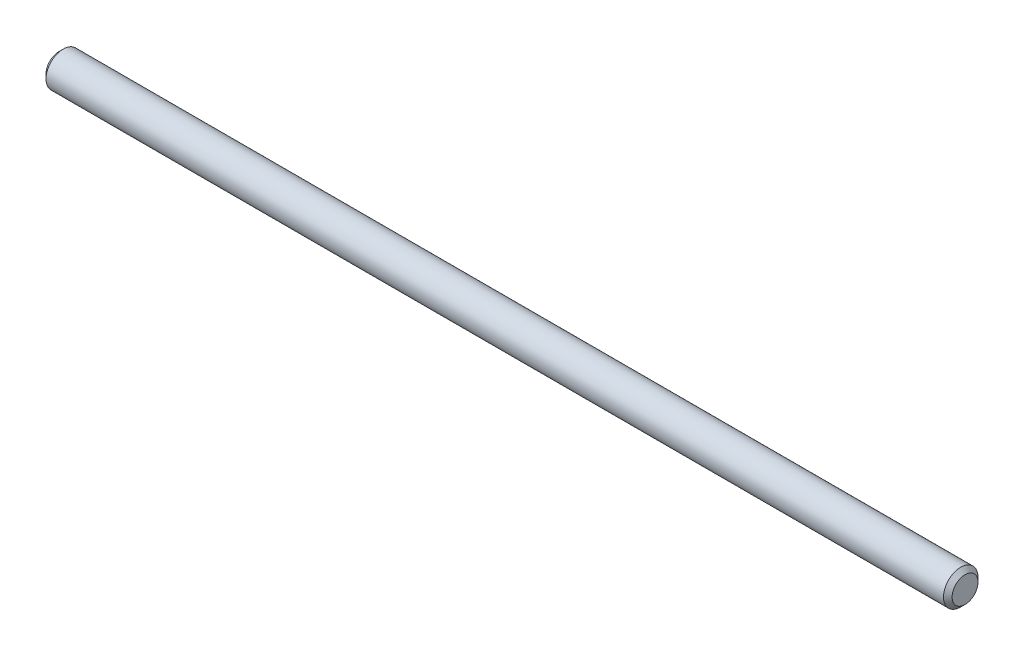
SolidWorks part; units mm, degrees
ref_plane "Front Plane" through (0, 0, 0) normal (0, 0, 1) x (1, 0, 0)
ref_plane "Top Plane" through (0, 0, 0) normal (0, 1, 0) x (1, 0, 0)
ref_plane "Right Plane" through (0, 0, 0) normal (1, 0, 0) x (0, 0, -1)
sketch "Sketch1" plane through (0, 0, 0) normal (1, 0, 0) x (0, 0, -1)
  circle A0 centre (0, 0) radius 2
extrude "Boss-Extrude1" add sketch "Sketch1" along normal blind 105
cosmetic thread "Cosmetic Thread1" parameters "D1"=16, "D2"=3.22
cosmetic thread "Cosmetic Thread2" parameters "D1"=8, "D2"=3.22
chamfer "Chamfer1" distance 0.5 angle 45 1 edges at (0, 0, -2)
chamfer "Chamfer2" distance 0.5 angle 45 1 edges at (105, 0, -2)
